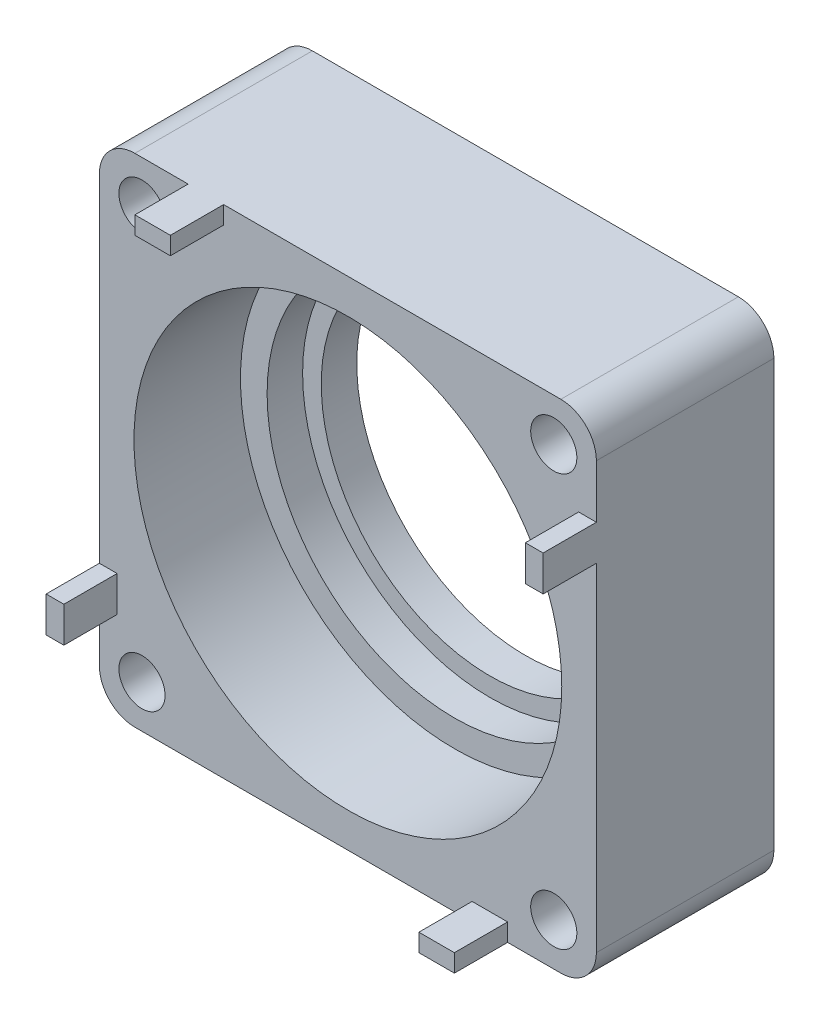
SolidWorks part; units mm, degrees
ref_plane "前视基准面" through (0, 0, 0) normal (0, 0, 1) x (1, 0, 0)
ref_plane "上视基准面" through (0, 0, 0) normal (0, 1, 0) x (1, 0, 0)
ref_plane "右视基准面" through (0, 0, 0) normal (1, 0, 0) x (0, 0, -1)
sketch "草图1" plane through (0, 0, 0) normal (0, 0, 1) x (1, 0, 0)
  line L1 (-14, 14) -> (14, 14)
  line L2 (-14, 14) -> (-14, -14)
  line L3 (-14, -14) -> (14, -14)
  line L4 (14, 14) -> (14, -14)
  line L5 (0, -14) -> (0, 14) construction
  line L6 (-14, 0) -> (14, 0) construction
  point P0 (0, 0)
  dimension "D1" = 28
  dimension "D2" = 28
extrude "凸台-拉伸1" add sketch "草图1" along normal blind 10
sketch "草图2" plane through (0, 0, 10) normal (0, 0, 1) x (1, 0, 0)
  circle A0 centre (0, 0) radius 9.5
  dimension "D1" = 19
extrude "切除-拉伸1" cut sketch "草图2" against normal through all
sketch "草图3" plane through (0, 0, 10) normal (0, 0, 1) x (1, 0, 0)
  circle A0 centre (0, 0) radius 10.55
  dimension "D1" = 21.1
extrude "切除-拉伸2" cut sketch "草图3" against normal offset from surface (8 mm away) 2 up to face at (9.5, 0, 0)
sketch "草图4" plane through (0, 0, 10) normal (0, 0, 1) x (1, 0, 0)
  circle A0 centre (0, 0) radius 12.05
  dimension "D1" = 24.1
extrude "切除-拉伸3" cut sketch "草图4" against normal offset from surface (6 mm away) 2 contours A0 up to face at (10.55, 0, 2)
fillet "圆角1" radius 2 4 edges at (-14, -14, 5) (14, -14, 5) (14, 14, 5) (-14, 14, 5)
sketch "草图5" plane through (0, 0, 10) normal (0, 0, 1) x (1, 0, 0)
  circle A0 centre (-11.6, 11.6) radius 1.3
  circle A3 centre (11.6, 11.6) radius 1.3
  circle A4 centre (11.6, -11.6) radius 1.3
  circle A5 centre (-11.6, -11.6) radius 1.3
  point P12 (0, 0)
  dimension "D1" = 2.6
  dimension "D2" = 11.6
  dimension "D3" = 11.6
  dimension "D4" = 4
extrude "切除-拉伸4" cut sketch "草图5" against normal through all
sketch "草图6" plane through (0, 0, 10) normal (0, 0, 1) x (1, 0, 0)
  line L0 (-14, 12) -> (-14, -12) construction
  line L1 (-14, -7) -> (-13, -7)
  line L2 (-14, -7) -> (-14, -9)
  line L3 (-14, -9) -> (-13, -9)
  line L4 (-13, -7) -> (-13, -9)
  line L6 (-12, -14) -> (12, -14) construction
  dimension "D1" = 1
  dimension "D2" = 2
  dimension "D3" = 5
extrude "凸台-拉伸2" add sketch "草图6" along normal blind 3
pattern_circular "阵列(圆周)1" count 4 over 360 about axis through (0, 0, 0) along (0, 0, 1) of "凸台-拉伸2"
